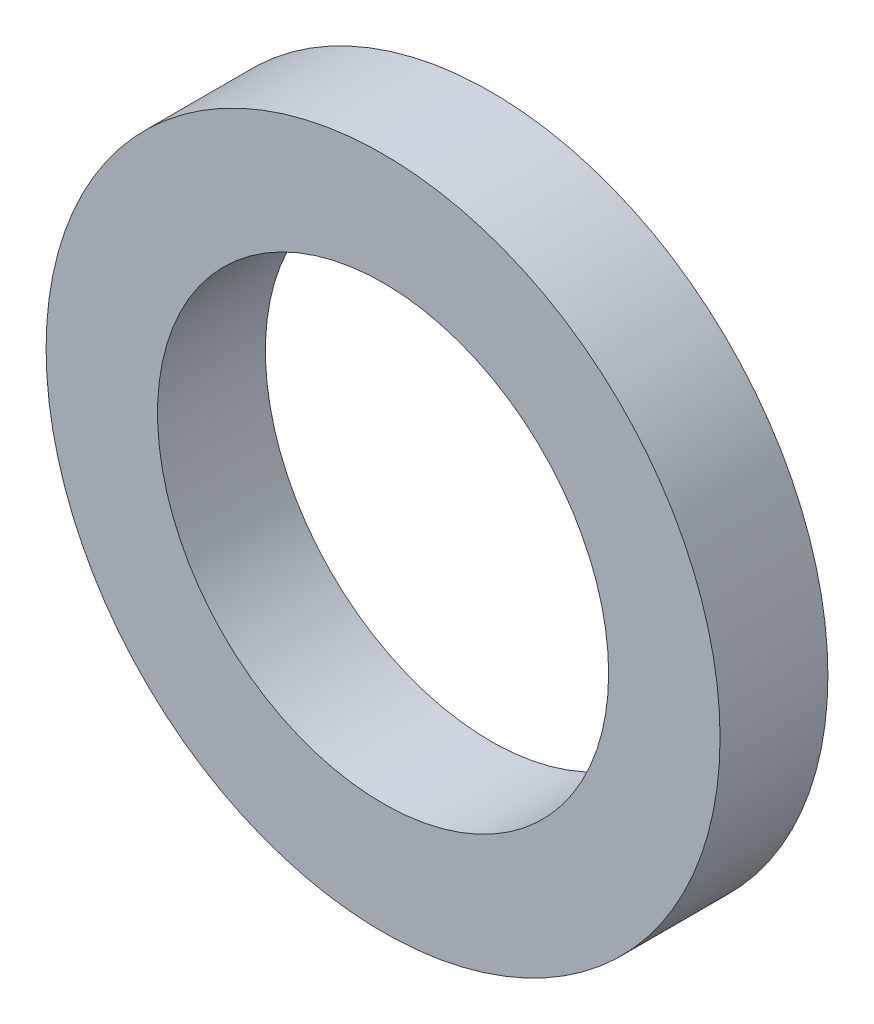
SolidWorks part; units mm, degrees
material "Wrought Stainless Steel"
ref_plane "Front Plane" through (0, 0, 0) normal (0, 0, 1) x (1, 0, 0)
ref_plane "Top Plane" through (0, 0, 0) normal (0, 1, 0) x (1, 0, 0)
ref_plane "Right Plane" through (0, 0, 0) normal (1, 0, 0) x (0, 0, -1)
sketch "Sketch2" plane through (0, 0, 0) normal (0, 0, 1) x (1, 0, 0)
  circle A0 centre (0, 0) radius 3.1877
  circle A1 centre (0, 0) radius 4.7625
  dimension "D1" = 6.3754
  dimension "D2" = 9.525
extrude "Boss-Extrude1" add sketch "Sketch2" along normal blind 1.524
